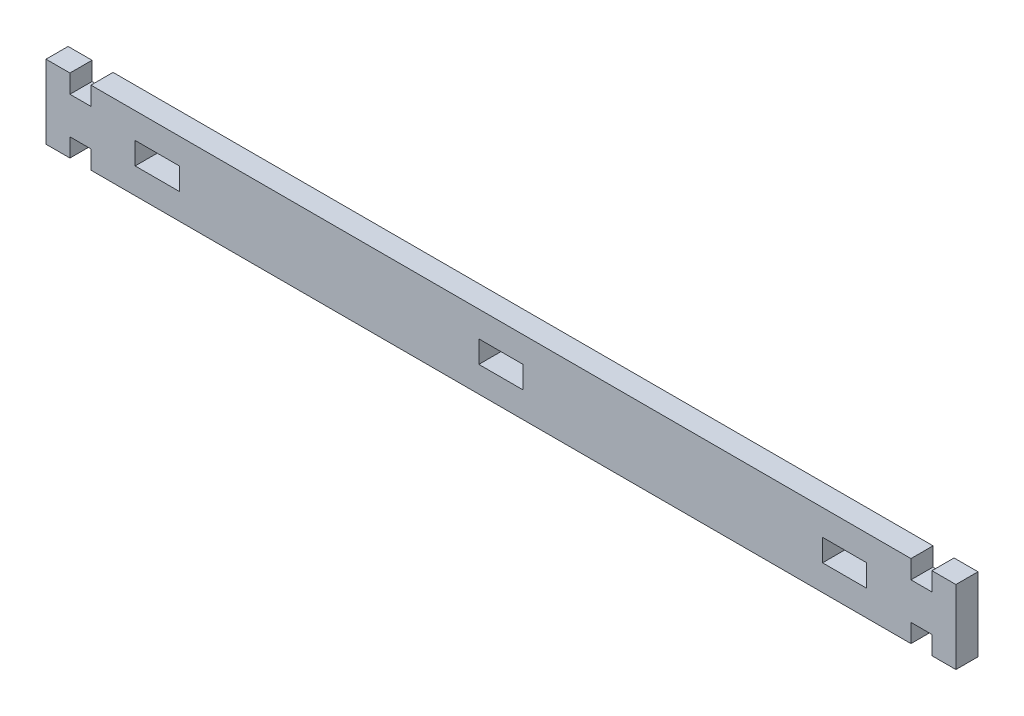
SolidWorks part; units mm, degrees
ref_plane "Front Plane" through (0, 0, 0) normal (0, 0, 1) x (1, 0, 0)
ref_plane "Top Plane" through (0, 0, 0) normal (0, 1, 0) x (1, 0, 0)
ref_plane "Right Plane" through (0, 0, 0) normal (1, 0, 0) x (0, 0, -1)
sketch "Sketch2" plane through (0, 0, 0) normal (0, 1, 0) x (1, 0, 0)
  line L0 (0, 0) -> (0, 6) construction
  dimension "D1" = 6
sketch "Sketch1" plane through (0, 0, 0) normal (0, 0, 1) x (1, 0, 0)
  line L0 (0, 0) -> (0, -10) construction
  line L1 (-123.5, -10) -> (123.5, -10)
  line L2 (-123.5, -10) -> (-123.5, 10)
  line L3 (-123.5, 10) -> (123.5, 10)
  line L4 (123.5, -10) -> (123.5, 10)
  line L5 (-123.5, -10) -> (123.5, 10) construction
  line L6 (-123.5, 10) -> (123.5, -10) construction
  line L7 (-123.5, 10) -> (-117, 10)
  line L8 (-123.5, 10) -> (-123.5, -10)
  line L9 (-123.5, -10) -> (-117, -10)
  line L10 (-117, 10) -> (-117, -10)
  line L11 (-117, -10) -> (-111.3, -10)
  line L12 (-117, -10) -> (-117, -5)
  line L13 (-117, -5) -> (-111.3, -5)
  line L14 (-111.3, -10) -> (-111.3, -5)
  line L15 (-117, 10) -> (-111.3, 10)
  line L16 (-117, 10) -> (-117, 5)
  line L17 (-117, 5) -> (-111.3, 5)
  line L18 (-111.3, 10) -> (-111.3, 5)
  line L19 (117, -5) -> (111.3, -5)
  line L20 (111.3, -10) -> (111.3, -5)
  line L21 (117, -10) -> (111.3, -10)
  line L22 (117, -10) -> (117, -5)
  line L23 (123.5, -10) -> (117, -10)
  line L24 (117, 10) -> (117, -10)
  line L25 (123.5, 10) -> (117, 10)
  line L26 (123.5, 10) -> (123.5, -10)
  line L27 (117, 5) -> (111.3, 5)
  line L28 (111.3, 10) -> (111.3, 5)
  line L29 (117, 10) -> (111.3, 10)
  line L30 (117, 10) -> (117, 5)
  line L31 (93.3, 0) -> (0, 0) construction
  line L32 (6, -3) -> (-6, -3)
  line L33 (6, -3) -> (6, 3)
  line L34 (6, 3) -> (-6, 3)
  line L35 (-6, -3) -> (-6, 3)
  line L36 (6, -3) -> (-6, 3) construction
  line L37 (6, 3) -> (-6, -3) construction
  line L38 (-99.3, -3) -> (-87.3, -3)
  line L39 (-99.3, -3) -> (-99.3, 3)
  line L40 (-99.3, 3) -> (-87.3, 3)
  line L41 (-87.3, -3) -> (-87.3, 3)
  line L42 (-99.3, -3) -> (-87.3, 3) construction
  line L43 (-99.3, 3) -> (-87.3, -3) construction
  line L44 (87.3, -3) -> (99.3, -3)
  line L45 (87.3, -3) -> (87.3, 3)
  line L46 (87.3, 3) -> (99.3, 3)
  line L47 (99.3, -3) -> (99.3, 3)
  line L48 (87.3, -3) -> (99.3, 3) construction
  line L49 (87.3, 3) -> (99.3, -3) construction
  line L50 (0, 0) -> (-93.3, 0) construction
  line L51 (99.3, 0) -> (111.3, 0) construction
  line L52 (111.3, 0) -> (111.3, -5) construction
  point P0 (0, 0)
  point P28 (-93.3, 0)
  point P33 (93.3, 0)
  dimension "D1" = 20
  dimension "D2" = 247
  dimension "D3" = 6.5
  dimension "D4" = 5.7
  dimension "D5" = 10
  dimension "D6" = 12
  dimension "D7" = 6
  dimension "D8" = 12
extrude "Boss-Extrude1" add sketch "Sketch1" against normal up to vertex (6 mm away) contours L10 L3 L2 L1 | L28 L3 L18 L17 L10 L13 L14 L1 L20 L19 L24 L27 | L3 L24 L22 L1 L4
equation "\"t_wood\"= 6' Thickness of the wood"
equation "\"t_glass\"= 2.5'Thickness of glass panels"
equation "\"w_glass\"= 248"
equation "\"h_glass\"= 167"
equation "\"h_food_internal\" = 60"
equation "\"entry_height\"= 20"
equation "\"entry diameter\"= 8"
equation "\"glass_bottom_overlap\"= 8"
equation "\"default_finger_size\"= 12"
equation "\"brood_depth\"= 42"
equation "\"outer_box_depth\" = \"brood_depth\" + ( 2 * \"t_glass\" ) + ( 2 * \"t_wood\" )"
equation "\"outer_box_width\"= \"w_glass\" + ( 2 * \"t_wood\" )"
equation "\"food_top_clearance\"= 10"
equation "\"outer_box_height\"= \"t_wood\" + \"h_glass\" + \"t_wood\" + \"h_food_internal\" + \"food_top_clearance\" + \"t_wood\""
equation "\"food_internal_depth\"= \"brood_depth\" + \"t_glass\" + \"t_glass\" - \"t_wood\" - \"t_wood\""
equation "\"food_channel_clearance_width\"= 14"
equation "\"bar_top_play\"= 4.5"
equation "\"bar_entry_angle\"= 10"
equation "\"bar_width\"= 20"
equation "\"entry_disk_play\"= 0.3"
equation "\"D1@Sketch2\"=\"t_wood\""
equation "\"D2@Sketch1\"=\"w_glass\"-1"
equation "\"D3@Sketch1\"=\"t_wood\"+0.5"
equation "\"D4@Sketch1\"=\"t_wood\"-0.3"
equation "\"D6@Sketch1\"=\"default_finger_size\""
equation "\"D7@Sketch1\"=\"t_wood\""
equation "\"D8@Sketch1\"=\"t_wood\"*2"
equation "\"D5@Sketch1\"=\"bar_width\"/2"
